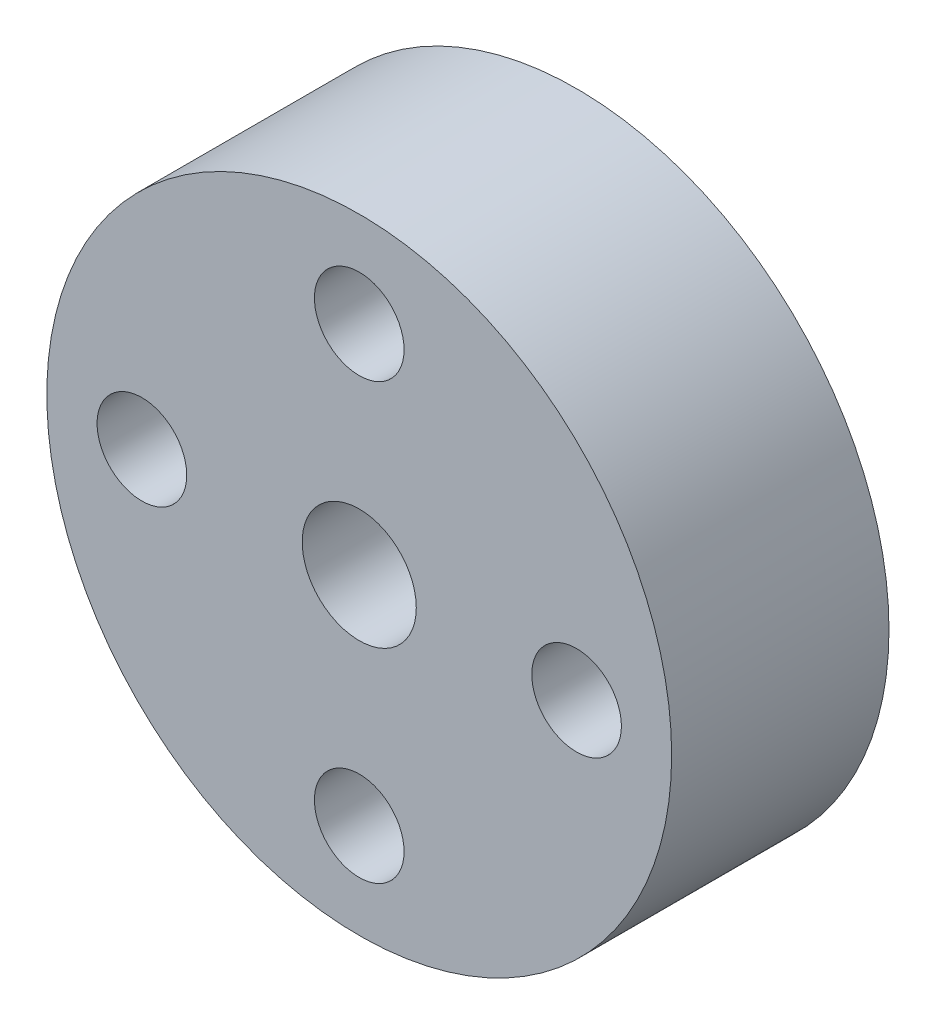
SolidWorks part; units mm, degrees
material "ABS"
ref_plane "前基準面" through (0, 0, 0) normal (0, 0, 1) x (1, 0, 0)
ref_plane "上基準面" through (0, 0, 0) normal (0, 1, 0) x (1, 0, 0)
ref_plane "右基準面" through (0, 0, 0) normal (1, 0, 0) x (0, 0, -1)
sketch "草圖1" plane through (0, 0, 0) normal (0, 0, 1) x (1, 0, 0)
  circle A0 centre (0, 0) radius 11.5
  circle A1 centre (0, 0) radius 8 construction
  circle A2 centre (0, 8) radius 1.65
  circle A3 centre (8, 0) radius 1.65
  circle A4 centre (0, -8) radius 1.65
  circle A5 centre (-8, 0) radius 1.65
  circle A6 centre (0, 0) radius 2.1
  dimension "D1" = 23
  dimension "D2" = 16
  dimension "D3" = 3.3
  dimension "D5" = 8
  dimension "D6" = 4.2
  dimension "D4" = 4
extrude "填料-伸長1" add sketch "草圖1" along normal blind 8
